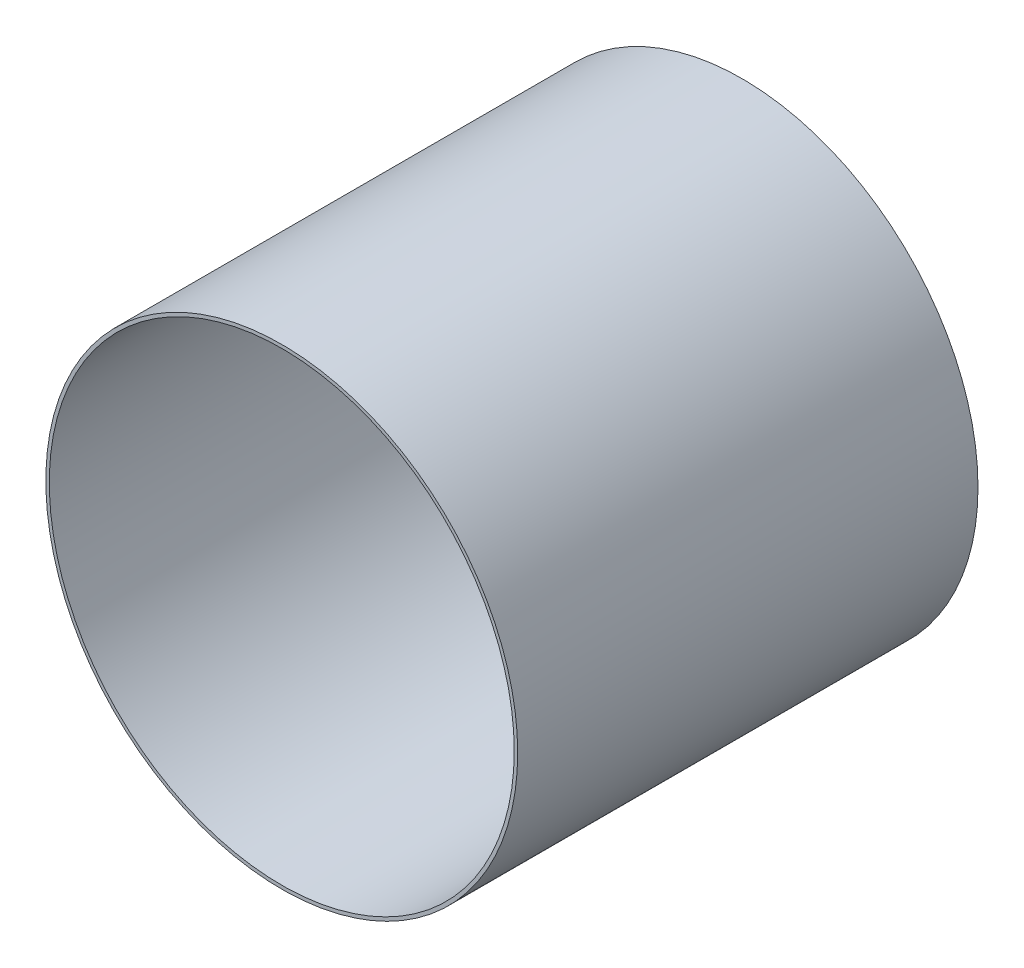
SolidWorks part; units mm, degrees
material "Titanio"
ref_plane "Piano frontale" through (0, 0, 0) normal (0, 0, 1) x (1, 0, 0)
ref_plane "Piano superiore" through (0, 0, 0) normal (0, 1, 0) x (1, 0, 0)
ref_plane "Piano destro" through (0, 0, 0) normal (1, 0, 0) x (0, 0, -1)
sketch "Schizzo1" plane through (0, 0, 0) normal (0, 0, 1) x (1, 0, 0)
  circle A0 centre (0, 0) radius 500
  circle A1 centre (0, 0) radius 492.7
  dimension "D1" = 1000
  dimension "D2" = 7.3
extrude "Estrusione-Estrusione1" add sketch "Schizzo1" along normal blind 975.5
